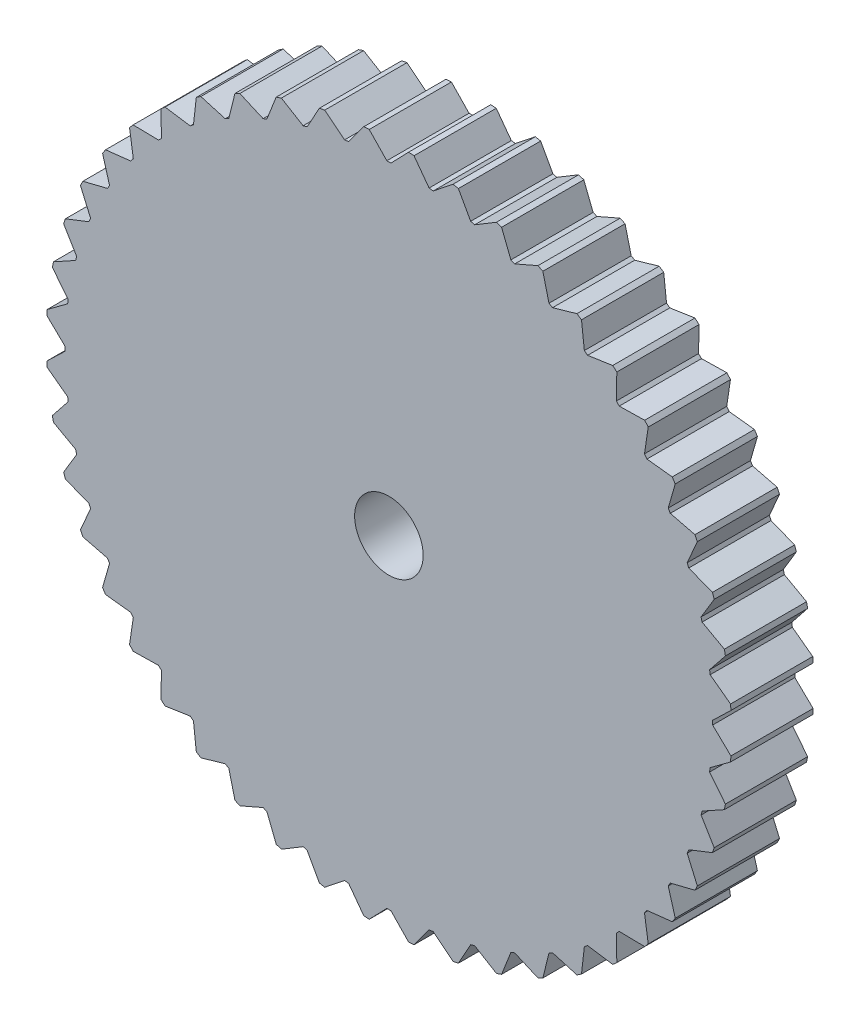
SolidWorks part; units mm, degrees
ref_plane "Front Plane" through (0, 0, 0) normal (0, 0, 1) x (1, 0, 0)
ref_plane "Top Plane" through (0, 0, 0) normal (0, 1, 0) x (1, 0, 0)
ref_plane "Right Plane" through (0, 0, 0) normal (1, 0, 0) x (0, 0, -1)
sketch "Sketch1" plane through (0, 0, 0) normal (0, 0, 1) x (1, 0, 0)
  line L0 (0, 0) -> (0, 50) construction
  line L1 (-3, 51) -> (-0.3, 47.3) construction
  line L2 (0.3, 47.3) -> (3, 51) construction
  line L3 (-0.3, 47.3) -> (0.3, 47.3) construction
  line L4 (-3, 51) -> (3, 51) construction
  line L5 (6.4713, 46.8562) -> (9.6312, 50.1721) construction
  line L6 (3.6825, 50.9553) -> (5.8765, 46.9345) construction
  line L7 (3.6825, 50.9553) -> (9.6312, 50.1721) construction
  line L8 (5.8765, 46.9345) -> (6.4713, 46.8562) construction
  line L9 (12.5319, 45.6106) -> (16.0975, 48.4858) construction
  line L10 (10.302, 50.0387) -> (11.9524, 45.7659) construction
  line L11 (10.302, 50.0387) -> (16.0975, 48.4858) construction
  line L12 (11.9524, 45.7659) -> (12.5319, 45.6106) construction
  line L13 (18.3781, 43.5847) -> (22.2885, 45.9698) construction
  line L14 (16.7452, 48.2659) -> (17.8238, 43.8143) construction
  line L15 (16.7452, 48.2659) -> (22.2885, 45.9698) construction
  line L16 (17.8238, 43.8143) -> (18.3781, 43.5847) construction
  line L17 (23.9098, 40.813) -> (28.0981, 42.6673) construction
  line L18 (22.9019, 45.6673) -> (23.3902, 41.113) construction
  line L19 (22.9019, 45.6673) -> (28.0981, 42.6673) construction
  line L20 (23.3902, 41.113) -> (23.9098, 40.813) construction
  line L21 (29.0324, 37.343) -> (33.4269, 38.6347) construction
  line L22 (28.6668, 42.2873) -> (28.5564, 37.7082) construction
  line L23 (28.6668, 42.2873) -> (33.4269, 38.6347) construction
  line L24 (28.5564, 37.7082) -> (29.0324, 37.343) construction
  line L25 (33.6583, 33.234) -> (38.1838, 33.9411) construction
  line L26 (33.9411, 38.1838) -> (33.234, 33.6583) construction
  line L27 (33.9411, 38.1838) -> (38.1838, 33.9411) construction
  line L28 (33.234, 33.6583) -> (33.6583, 33.234) construction
  line L29 (37.7082, 28.5564) -> (42.2873, 28.6668) construction
  line L30 (38.6347, 33.4269) -> (37.343, 29.0324) construction
  line L31 (38.6347, 33.4269) -> (42.2873, 28.6668) construction
  line L32 (37.343, 29.0324) -> (37.7082, 28.5564) construction
  line L33 (41.113, 23.3902) -> (45.6673, 22.9019) construction
  line L34 (42.6673, 28.0981) -> (40.813, 23.9098) construction
  line L35 (42.6673, 28.0981) -> (45.6673, 22.9019) construction
  line L36 (40.813, 23.9098) -> (41.113, 23.3902) construction
  line L37 (43.8143, 17.8238) -> (48.2659, 16.7452) construction
  line L38 (45.9698, 22.2885) -> (43.5847, 18.3781) construction
  line L39 (45.9698, 22.2885) -> (48.2659, 16.7452) construction
  line L40 (43.5847, 18.3781) -> (43.8143, 17.8238) construction
  line L41 (45.7659, 11.9524) -> (50.0387, 10.302) construction
  line L42 (48.4858, 16.0975) -> (45.6106, 12.5319) construction
  line L43 (48.4858, 16.0975) -> (50.0387, 10.302) construction
  line L44 (45.6106, 12.5319) -> (45.7659, 11.9524) construction
  line L45 (46.9345, 5.8765) -> (50.9553, 3.6825) construction
  line L46 (50.1721, 9.6312) -> (46.8562, 6.4713) construction
  line L47 (50.1721, 9.6312) -> (50.9553, 3.6825) construction
  line L48 (46.8562, 6.4713) -> (46.9345, 5.8765) construction
  line L49 (47.3, -0.3) -> (51, -3) construction
  line L50 (51, 3) -> (47.3, 0.3) construction
  line L51 (51, 3) -> (51, -3) construction
  line L52 (47.3, 0.3) -> (47.3, -0.3) construction
  line L53 (46.8562, -6.4713) -> (50.1721, -9.6312) construction
  line L54 (50.9553, -3.6825) -> (46.9345, -5.8765) construction
  line L55 (50.9553, -3.6825) -> (50.1721, -9.6312) construction
  line L56 (46.9345, -5.8765) -> (46.8562, -6.4713) construction
  line L57 (45.6106, -12.5319) -> (48.4858, -16.0975) construction
  line L58 (50.0387, -10.302) -> (45.7659, -11.9524) construction
  line L59 (50.0387, -10.302) -> (48.4858, -16.0975) construction
  line L60 (45.7659, -11.9524) -> (45.6106, -12.5319) construction
  line L61 (43.5847, -18.3781) -> (45.9698, -22.2885) construction
  line L62 (48.2659, -16.7452) -> (43.8143, -17.8238) construction
  line L63 (48.2659, -16.7452) -> (45.9698, -22.2885) construction
  line L64 (43.8143, -17.8238) -> (43.5847, -18.3781) construction
  line L65 (40.813, -23.9098) -> (42.6673, -28.0981) construction
  line L66 (45.6673, -22.9019) -> (41.113, -23.3902) construction
  line L67 (45.6673, -22.9019) -> (42.6673, -28.0981) construction
  line L68 (41.113, -23.3902) -> (40.813, -23.9098) construction
  line L69 (37.343, -29.0324) -> (38.6347, -33.4269) construction
  line L70 (42.2873, -28.6668) -> (37.7082, -28.5564) construction
  line L71 (42.2873, -28.6668) -> (38.6347, -33.4269) construction
  line L72 (37.7082, -28.5564) -> (37.343, -29.0324) construction
  line L73 (33.234, -33.6583) -> (33.9411, -38.1838) construction
  line L74 (38.1838, -33.9411) -> (33.6583, -33.234) construction
  line L75 (38.1838, -33.9411) -> (33.9411, -38.1838) construction
  line L76 (33.6583, -33.234) -> (33.234, -33.6583) construction
  line L77 (28.5564, -37.7082) -> (28.6668, -42.2873) construction
  line L78 (33.4269, -38.6347) -> (29.0324, -37.343) construction
  line L79 (33.4269, -38.6347) -> (28.6668, -42.2873) construction
  line L80 (29.0324, -37.343) -> (28.5564, -37.7082) construction
  line L81 (23.3902, -41.113) -> (22.9019, -45.6673) construction
  line L82 (28.0981, -42.6673) -> (23.9098, -40.813) construction
  line L83 (28.0981, -42.6673) -> (22.9019, -45.6673) construction
  line L84 (23.9098, -40.813) -> (23.3902, -41.113) construction
  line L85 (17.8238, -43.8143) -> (16.7452, -48.2659) construction
  line L86 (22.2885, -45.9698) -> (18.3781, -43.5847) construction
  line L87 (22.2885, -45.9698) -> (16.7452, -48.2659) construction
  line L88 (18.3781, -43.5847) -> (17.8238, -43.8143) construction
  line L89 (11.9524, -45.7659) -> (10.302, -50.0387) construction
  line L90 (16.0975, -48.4858) -> (12.5319, -45.6106) construction
  line L91 (16.0975, -48.4858) -> (10.302, -50.0387) construction
  line L92 (12.5319, -45.6106) -> (11.9524, -45.7659) construction
  line L93 (5.8765, -46.9345) -> (3.6825, -50.9553) construction
  line L94 (9.6312, -50.1721) -> (6.4713, -46.8562) construction
  line L95 (9.6312, -50.1721) -> (3.6825, -50.9553) construction
  line L96 (6.4713, -46.8562) -> (5.8765, -46.9345) construction
  line L97 (-0.3, -47.3) -> (-3, -51) construction
  line L98 (3, -51) -> (0.3, -47.3) construction
  line L99 (3, -51) -> (-3, -51) construction
  line L100 (0.3, -47.3) -> (-0.3, -47.3) construction
  line L101 (-6.4713, -46.8562) -> (-9.6312, -50.1721) construction
  line L102 (-3.6825, -50.9553) -> (-5.8765, -46.9345) construction
  line L103 (-3.6825, -50.9553) -> (-9.6312, -50.1721) construction
  line L104 (-5.8765, -46.9345) -> (-6.4713, -46.8562) construction
  line L105 (-12.5319, -45.6106) -> (-16.0975, -48.4858) construction
  line L106 (-10.302, -50.0387) -> (-11.9524, -45.7659) construction
  line L107 (-10.302, -50.0387) -> (-16.0975, -48.4858) construction
  line L108 (-11.9524, -45.7659) -> (-12.5319, -45.6106) construction
  line L109 (-18.3781, -43.5847) -> (-22.2885, -45.9698) construction
  line L110 (-16.7452, -48.2659) -> (-17.8238, -43.8143) construction
  line L111 (-16.7452, -48.2659) -> (-22.2885, -45.9698) construction
  line L112 (-17.8238, -43.8143) -> (-18.3781, -43.5847) construction
  line L113 (-23.9098, -40.813) -> (-28.0981, -42.6673) construction
  line L114 (-22.9019, -45.6673) -> (-23.3902, -41.113) construction
  line L115 (-22.9019, -45.6673) -> (-28.0981, -42.6673) construction
  line L116 (-23.3902, -41.113) -> (-23.9098, -40.813) construction
  line L117 (-29.0324, -37.343) -> (-33.4269, -38.6347) construction
  line L118 (-28.6668, -42.2873) -> (-28.5564, -37.7082) construction
  line L119 (-28.6668, -42.2873) -> (-33.4269, -38.6347) construction
  line L120 (-28.5564, -37.7082) -> (-29.0324, -37.343) construction
  line L121 (-33.6583, -33.234) -> (-38.1838, -33.9411) construction
  line L122 (-33.9411, -38.1838) -> (-33.234, -33.6583) construction
  line L123 (-33.9411, -38.1838) -> (-38.1838, -33.9411) construction
  line L124 (-33.234, -33.6583) -> (-33.6583, -33.234) construction
  line L125 (-37.7082, -28.5564) -> (-42.2873, -28.6668) construction
  line L126 (-38.6347, -33.4269) -> (-37.343, -29.0324) construction
  line L127 (-38.6347, -33.4269) -> (-42.2873, -28.6668) construction
  line L128 (-37.343, -29.0324) -> (-37.7082, -28.5564) construction
  line L129 (-41.113, -23.3902) -> (-45.6673, -22.9019) construction
  line L130 (-42.6673, -28.0981) -> (-40.813, -23.9098) construction
  line L131 (-42.6673, -28.0981) -> (-45.6673, -22.9019) construction
  line L132 (-40.813, -23.9098) -> (-41.113, -23.3902) construction
  line L133 (-43.8143, -17.8238) -> (-48.2659, -16.7452) construction
  line L134 (-45.9698, -22.2885) -> (-43.5847, -18.3781) construction
  line L135 (-45.9698, -22.2885) -> (-48.2659, -16.7452) construction
  line L136 (-43.5847, -18.3781) -> (-43.8143, -17.8238) construction
  line L137 (-45.7659, -11.9524) -> (-50.0387, -10.302) construction
  line L138 (-48.4858, -16.0975) -> (-45.6106, -12.5319) construction
  line L139 (-48.4858, -16.0975) -> (-50.0387, -10.302) construction
  line L140 (-45.6106, -12.5319) -> (-45.7659, -11.9524) construction
  line L141 (-46.9345, -5.8765) -> (-50.9553, -3.6825) construction
  line L142 (-50.1721, -9.6312) -> (-46.8562, -6.4713) construction
  line L143 (-50.1721, -9.6312) -> (-50.9553, -3.6825) construction
  line L144 (-46.8562, -6.4713) -> (-46.9345, -5.8765) construction
  line L145 (-47.3, 0.3) -> (-51, 3) construction
  line L146 (-51, -3) -> (-47.3, -0.3) construction
  line L147 (-51, -3) -> (-51, 3) construction
  line L148 (-47.3, -0.3) -> (-47.3, 0.3) construction
  line L149 (-46.8562, 6.4713) -> (-50.1721, 9.6312) construction
  line L150 (-50.9553, 3.6825) -> (-46.9345, 5.8765) construction
  line L151 (-50.9553, 3.6825) -> (-50.1721, 9.6312) construction
  line L152 (-46.9345, 5.8765) -> (-46.8562, 6.4713) construction
  line L153 (-45.6106, 12.5319) -> (-48.4858, 16.0975) construction
  line L154 (-50.0387, 10.302) -> (-45.7659, 11.9524) construction
  line L155 (-50.0387, 10.302) -> (-48.4858, 16.0975) construction
  line L156 (-45.7659, 11.9524) -> (-45.6106, 12.5319) construction
  line L157 (-43.5847, 18.3781) -> (-45.9698, 22.2885) construction
  line L158 (-48.2659, 16.7452) -> (-43.8143, 17.8238) construction
  line L159 (-48.2659, 16.7452) -> (-45.9698, 22.2885) construction
  line L160 (-43.8143, 17.8238) -> (-43.5847, 18.3781) construction
  line L161 (-40.813, 23.9098) -> (-42.6673, 28.0981) construction
  line L162 (-45.6673, 22.9019) -> (-41.113, 23.3902) construction
  line L163 (-45.6673, 22.9019) -> (-42.6673, 28.0981) construction
  line L164 (-41.113, 23.3902) -> (-40.813, 23.9098) construction
  line L165 (-37.343, 29.0324) -> (-38.6347, 33.4269) construction
  line L166 (-42.2873, 28.6668) -> (-37.7082, 28.5564) construction
  line L167 (-42.2873, 28.6668) -> (-38.6347, 33.4269) construction
  line L168 (-37.7082, 28.5564) -> (-37.343, 29.0324) construction
  line L169 (-33.234, 33.6583) -> (-33.9411, 38.1838) construction
  line L170 (-38.1838, 33.9411) -> (-33.6583, 33.234) construction
  line L171 (-38.1838, 33.9411) -> (-33.9411, 38.1838) construction
  line L172 (-33.6583, 33.234) -> (-33.234, 33.6583) construction
  line L173 (-28.5564, 37.7082) -> (-28.6668, 42.2873) construction
  line L174 (-33.4269, 38.6347) -> (-29.0324, 37.343) construction
  line L175 (-33.4269, 38.6347) -> (-28.6668, 42.2873) construction
  line L176 (-29.0324, 37.343) -> (-28.5564, 37.7082) construction
  line L177 (-23.3902, 41.113) -> (-22.9019, 45.6673) construction
  line L178 (-28.0981, 42.6673) -> (-23.9098, 40.813) construction
  line L179 (-28.0981, 42.6673) -> (-22.9019, 45.6673) construction
  line L180 (-23.9098, 40.813) -> (-23.3902, 41.113) construction
  line L181 (-17.8238, 43.8143) -> (-16.7452, 48.2659) construction
  line L182 (-22.2885, 45.9698) -> (-18.3781, 43.5847) construction
  line L183 (-22.2885, 45.9698) -> (-16.7452, 48.2659) construction
  line L184 (-18.3781, 43.5847) -> (-17.8238, 43.8143) construction
  line L185 (-11.9524, 45.7659) -> (-10.302, 50.0387) construction
  line L186 (-16.0975, 48.4858) -> (-12.5319, 45.6106) construction
  line L187 (-16.0975, 48.4858) -> (-10.302, 50.0387) construction
  line L188 (-12.5319, 45.6106) -> (-11.9524, 45.7659) construction
  line L189 (-5.8765, 46.9345) -> (-3.6825, 50.9553) construction
  line L190 (-9.6312, 50.1721) -> (-6.4713, 46.8562) construction
  line L191 (-9.6312, 50.1721) -> (-3.6825, 50.9553) construction
  line L192 (-6.4713, 46.8562) -> (-5.8765, 46.9345) construction
  circle A0 centre (0, 0) radius 50
  circle A1 centre (0, 0) radius 5
  point P200 (0, 0)
  dimension "D1" = 10
  dimension "D2" = 100
  dimension "D3" = 0.6
  dimension "D4" = 6
  dimension "D5" = 3.7
  dimension "D6" = 1
  dimension "D7" = 48
extrude "Boss-Extrude1" add sketch "Sketch1" along normal blind 12 contours A1 | A0
sketch "Sketch2" plane through (0, 0, 12) normal (0, 0, 1) x (1, 0, 0)
  line L0 (0, 0) -> (0, 50) construction
  line L1 (-3, 50.05) -> (-0.3, 47.25)
  line L2 (0.3, 47.25) -> (3, 50.05)
  line L3 (-0.3, 47.25) -> (0.3, 47.25)
  line L4 (-3, 50.05) -> (3, 50.05)
  line L5 (6.4648, 46.8066) -> (9.5072, 49.2302)
  line L6 (5.8699, 46.8849) -> (6.4648, 46.8066)
  line L7 (3.5585, 50.0134) -> (5.8699, 46.8849)
  line L8 (3.5585, 50.0134) -> (9.5072, 49.2302)
  line L9 (12.519, 45.5623) -> (15.8517, 47.5681)
  line L10 (11.9394, 45.7176) -> (12.519, 45.5623)
  line L11 (10.0561, 49.121) -> (11.9394, 45.7176)
  line L12 (10.0561, 49.121) -> (15.8517, 47.5681)
  line L13 (18.359, 43.5385) -> (21.9249, 45.0921)
  line L14 (17.8046, 43.7681) -> (18.359, 43.5385)
  line L15 (16.3817, 47.3882) -> (17.8046, 43.7681)
  line L16 (16.3817, 47.3882) -> (21.9249, 45.0921)
  line L17 (23.8848, 40.7697) -> (27.6231, 41.8446)
  line L18 (23.3652, 41.0697) -> (23.8848, 40.7697)
  line L19 (22.4269, 44.8446) -> (23.3652, 41.0697)
  line L20 (22.4269, 44.8446) -> (27.6231, 41.8446)
  line L21 (29.002, 37.3033) -> (32.8486, 37.8811)
  line L22 (28.526, 37.6686) -> (29.002, 37.3033)
  line L23 (28.0884, 41.5336) -> (28.526, 37.6686)
  line L24 (28.0884, 41.5336) -> (32.8486, 37.8811)
  line L25 (33.6229, 33.1987) -> (37.512, 33.2694)
  line L26 (33.1987, 33.6229) -> (33.6229, 33.1987)
  line L27 (33.2694, 37.512) -> (33.1987, 33.6229)
  line L28 (33.2694, 37.512) -> (37.512, 33.2694)
  line L29 (37.6686, 28.526) -> (41.5336, 28.0884)
  line L30 (37.3033, 29.002) -> (37.6686, 28.526)
  line L31 (37.8811, 32.8486) -> (37.3033, 29.002)
  line L32 (37.8811, 32.8486) -> (41.5336, 28.0884)
  line L33 (41.0697, 23.3652) -> (44.8446, 22.4269)
  line L34 (40.7697, 23.8848) -> (41.0697, 23.3652)
  line L35 (41.8446, 27.6231) -> (40.7697, 23.8848)
  line L36 (41.8446, 27.6231) -> (44.8446, 22.4269)
  line L37 (43.7681, 17.8046) -> (47.3882, 16.3817)
  line L38 (43.5385, 18.359) -> (43.7681, 17.8046)
  line L39 (45.0921, 21.9249) -> (43.5385, 18.359)
  line L40 (45.0921, 21.9249) -> (47.3882, 16.3817)
  line L41 (45.7176, 11.9394) -> (49.121, 10.0561)
  line L42 (45.5623, 12.519) -> (45.7176, 11.9394)
  line L43 (47.5681, 15.8517) -> (45.5623, 12.519)
  line L44 (47.5681, 15.8517) -> (49.121, 10.0561)
  line L45 (46.8849, 5.8699) -> (50.0134, 3.5585)
  line L46 (46.8066, 6.4648) -> (46.8849, 5.8699)
  line L47 (49.2302, 9.5072) -> (46.8066, 6.4648)
  line L48 (49.2302, 9.5072) -> (50.0134, 3.5585)
  line L49 (47.25, -0.3) -> (50.05, -3)
  line L50 (47.25, 0.3) -> (47.25, -0.3)
  line L51 (50.05, 3) -> (47.25, 0.3)
  line L52 (50.05, 3) -> (50.05, -3)
  line L53 (46.8066, -6.4648) -> (49.2302, -9.5072)
  line L54 (46.8849, -5.8699) -> (46.8066, -6.4648)
  line L55 (50.0134, -3.5585) -> (46.8849, -5.8699)
  line L56 (50.0134, -3.5585) -> (49.2302, -9.5072)
  line L57 (45.5623, -12.519) -> (47.5681, -15.8517)
  line L58 (45.7176, -11.9394) -> (45.5623, -12.519)
  line L59 (49.121, -10.0561) -> (45.7176, -11.9394)
  line L60 (49.121, -10.0561) -> (47.5681, -15.8517)
  line L61 (43.5385, -18.359) -> (45.0921, -21.9249)
  line L62 (43.7681, -17.8046) -> (43.5385, -18.359)
  line L63 (47.3882, -16.3817) -> (43.7681, -17.8046)
  line L64 (47.3882, -16.3817) -> (45.0921, -21.9249)
  line L65 (40.7697, -23.8848) -> (41.8446, -27.6231)
  line L66 (41.0697, -23.3652) -> (40.7697, -23.8848)
  line L67 (44.8446, -22.4269) -> (41.0697, -23.3652)
  line L68 (44.8446, -22.4269) -> (41.8446, -27.6231)
  line L69 (37.3033, -29.002) -> (37.8811, -32.8486)
  line L70 (37.6686, -28.526) -> (37.3033, -29.002)
  line L71 (41.5336, -28.0884) -> (37.6686, -28.526)
  line L72 (41.5336, -28.0884) -> (37.8811, -32.8486)
  line L73 (33.1987, -33.6229) -> (33.2694, -37.512)
  line L74 (33.6229, -33.1987) -> (33.1987, -33.6229)
  line L75 (37.512, -33.2694) -> (33.6229, -33.1987)
  line L76 (37.512, -33.2694) -> (33.2694, -37.512)
  line L77 (28.526, -37.6686) -> (28.0884, -41.5336)
  line L78 (29.002, -37.3033) -> (28.526, -37.6686)
  line L79 (32.8486, -37.8811) -> (29.002, -37.3033)
  line L80 (32.8486, -37.8811) -> (28.0884, -41.5336)
  line L81 (23.3652, -41.0697) -> (22.4269, -44.8446)
  line L82 (23.8848, -40.7697) -> (23.3652, -41.0697)
  line L83 (27.6231, -41.8446) -> (23.8848, -40.7697)
  line L84 (27.6231, -41.8446) -> (22.4269, -44.8446)
  line L85 (17.8046, -43.7681) -> (16.3817, -47.3882)
  line L86 (18.359, -43.5385) -> (17.8046, -43.7681)
  line L87 (21.9249, -45.0921) -> (18.359, -43.5385)
  line L88 (21.9249, -45.0921) -> (16.3817, -47.3882)
  line L89 (11.9394, -45.7176) -> (10.0561, -49.121)
  line L90 (12.519, -45.5623) -> (11.9394, -45.7176)
  line L91 (15.8517, -47.5681) -> (12.519, -45.5623)
  line L92 (15.8517, -47.5681) -> (10.0561, -49.121)
  line L93 (5.8699, -46.8849) -> (3.5585, -50.0134)
  line L94 (6.4648, -46.8066) -> (5.8699, -46.8849)
  line L95 (9.5072, -49.2302) -> (6.4648, -46.8066)
  line L96 (9.5072, -49.2302) -> (3.5585, -50.0134)
  line L97 (-0.3, -47.25) -> (-3, -50.05)
  line L98 (0.3, -47.25) -> (-0.3, -47.25)
  line L99 (3, -50.05) -> (0.3, -47.25)
  line L100 (3, -50.05) -> (-3, -50.05)
  line L101 (-6.4648, -46.8066) -> (-9.5072, -49.2302)
  line L102 (-5.8699, -46.8849) -> (-6.4648, -46.8066)
  line L103 (-3.5585, -50.0134) -> (-5.8699, -46.8849)
  line L104 (-3.5585, -50.0134) -> (-9.5072, -49.2302)
  line L105 (-12.519, -45.5623) -> (-15.8517, -47.5681)
  line L106 (-11.9394, -45.7176) -> (-12.519, -45.5623)
  line L107 (-10.0561, -49.121) -> (-11.9394, -45.7176)
  line L108 (-10.0561, -49.121) -> (-15.8517, -47.5681)
  line L109 (-18.359, -43.5385) -> (-21.9249, -45.0921)
  line L110 (-17.8046, -43.7681) -> (-18.359, -43.5385)
  line L111 (-16.3817, -47.3882) -> (-17.8046, -43.7681)
  line L112 (-16.3817, -47.3882) -> (-21.9249, -45.0921)
  line L113 (-23.8848, -40.7697) -> (-27.6231, -41.8446)
  line L114 (-23.3652, -41.0697) -> (-23.8848, -40.7697)
  line L115 (-22.4269, -44.8446) -> (-23.3652, -41.0697)
  line L116 (-22.4269, -44.8446) -> (-27.6231, -41.8446)
  line L117 (-29.002, -37.3033) -> (-32.8486, -37.8811)
  line L118 (-28.526, -37.6686) -> (-29.002, -37.3033)
  line L119 (-28.0884, -41.5336) -> (-28.526, -37.6686)
  line L120 (-28.0884, -41.5336) -> (-32.8486, -37.8811)
  line L121 (-33.6229, -33.1987) -> (-37.512, -33.2694)
  line L122 (-33.1987, -33.6229) -> (-33.6229, -33.1987)
  line L123 (-33.2694, -37.512) -> (-33.1987, -33.6229)
  line L124 (-33.2694, -37.512) -> (-37.512, -33.2694)
  line L125 (-37.6686, -28.526) -> (-41.5336, -28.0884)
  line L126 (-37.3033, -29.002) -> (-37.6686, -28.526)
  line L127 (-37.8811, -32.8486) -> (-37.3033, -29.002)
  line L128 (-37.8811, -32.8486) -> (-41.5336, -28.0884)
  line L129 (-41.0697, -23.3652) -> (-44.8446, -22.4269)
  line L130 (-40.7697, -23.8848) -> (-41.0697, -23.3652)
  line L131 (-41.8446, -27.6231) -> (-40.7697, -23.8848)
  line L132 (-41.8446, -27.6231) -> (-44.8446, -22.4269)
  line L133 (-43.7681, -17.8046) -> (-47.3882, -16.3817)
  line L134 (-43.5385, -18.359) -> (-43.7681, -17.8046)
  line L135 (-45.0921, -21.9249) -> (-43.5385, -18.359)
  line L136 (-45.0921, -21.9249) -> (-47.3882, -16.3817)
  line L137 (-45.7176, -11.9394) -> (-49.121, -10.0561)
  line L138 (-45.5623, -12.519) -> (-45.7176, -11.9394)
  line L139 (-47.5681, -15.8517) -> (-45.5623, -12.519)
  line L140 (-47.5681, -15.8517) -> (-49.121, -10.0561)
  line L141 (-46.8849, -5.8699) -> (-50.0134, -3.5585)
  line L142 (-46.8066, -6.4648) -> (-46.8849, -5.8699)
  line L143 (-49.2302, -9.5072) -> (-46.8066, -6.4648)
  line L144 (-49.2302, -9.5072) -> (-50.0134, -3.5585)
  line L145 (-47.25, 0.3) -> (-50.05, 3)
  line L146 (-47.25, -0.3) -> (-47.25, 0.3)
  line L147 (-50.05, -3) -> (-47.25, -0.3)
  line L148 (-50.05, -3) -> (-50.05, 3)
  line L149 (-46.8066, 6.4648) -> (-49.2302, 9.5072)
  line L150 (-46.8849, 5.8699) -> (-46.8066, 6.4648)
  line L151 (-50.0134, 3.5585) -> (-46.8849, 5.8699)
  line L152 (-50.0134, 3.5585) -> (-49.2302, 9.5072)
  line L153 (-45.5623, 12.519) -> (-47.5681, 15.8517)
  line L154 (-45.7176, 11.9394) -> (-45.5623, 12.519)
  line L155 (-49.121, 10.0561) -> (-45.7176, 11.9394)
  line L156 (-49.121, 10.0561) -> (-47.5681, 15.8517)
  line L157 (-43.5385, 18.359) -> (-45.0921, 21.9249)
  line L158 (-43.7681, 17.8046) -> (-43.5385, 18.359)
  line L159 (-47.3882, 16.3817) -> (-43.7681, 17.8046)
  line L160 (-47.3882, 16.3817) -> (-45.0921, 21.9249)
  line L161 (-40.7697, 23.8848) -> (-41.8446, 27.6231)
  line L162 (-41.0697, 23.3652) -> (-40.7697, 23.8848)
  line L163 (-44.8446, 22.4269) -> (-41.0697, 23.3652)
  line L164 (-44.8446, 22.4269) -> (-41.8446, 27.6231)
  line L165 (-37.3033, 29.002) -> (-37.8811, 32.8486)
  line L166 (-37.6686, 28.526) -> (-37.3033, 29.002)
  line L167 (-41.5336, 28.0884) -> (-37.6686, 28.526)
  line L168 (-41.5336, 28.0884) -> (-37.8811, 32.8486)
  line L169 (-33.1987, 33.6229) -> (-33.2694, 37.512)
  line L170 (-33.6229, 33.1987) -> (-33.1987, 33.6229)
  line L171 (-37.512, 33.2694) -> (-33.6229, 33.1987)
  line L172 (-37.512, 33.2694) -> (-33.2694, 37.512)
  line L173 (-28.526, 37.6686) -> (-28.0884, 41.5336)
  line L174 (-29.002, 37.3033) -> (-28.526, 37.6686)
  line L175 (-32.8486, 37.8811) -> (-29.002, 37.3033)
  line L176 (-32.8486, 37.8811) -> (-28.0884, 41.5336)
  line L177 (-23.3652, 41.0697) -> (-22.4269, 44.8446)
  line L178 (-23.8848, 40.7697) -> (-23.3652, 41.0697)
  line L179 (-27.6231, 41.8446) -> (-23.8848, 40.7697)
  line L180 (-27.6231, 41.8446) -> (-22.4269, 44.8446)
  line L181 (-17.8046, 43.7681) -> (-16.3817, 47.3882)
  line L182 (-18.359, 43.5385) -> (-17.8046, 43.7681)
  line L183 (-21.9249, 45.0921) -> (-18.359, 43.5385)
  line L184 (-21.9249, 45.0921) -> (-16.3817, 47.3882)
  line L185 (-11.9394, 45.7176) -> (-10.0561, 49.121)
  line L186 (-12.519, 45.5623) -> (-11.9394, 45.7176)
  line L187 (-15.8517, 47.5681) -> (-12.519, 45.5623)
  line L188 (-15.8517, 47.5681) -> (-10.0561, 49.121)
  line L189 (-5.8699, 46.8849) -> (-3.5585, 50.0134)
  line L190 (-6.4648, 46.8066) -> (-5.8699, 46.8849)
  line L191 (-9.5072, 49.2302) -> (-6.4648, 46.8066)
  line L192 (-9.5072, 49.2302) -> (-3.5585, 50.0134)
  circle A0 centre (0, 0) radius 50 construction
  point P199 (0, 0)
  dimension "D1" = 48
  dimension "D2" = 100
  dimension "D3" = 0.6
  dimension "D4" = 6
  dimension "D5" = 2.8
  dimension "D6" = 0.05
extrude "Cut-Extrude1" cut sketch "Sketch2" against normal blind 12
